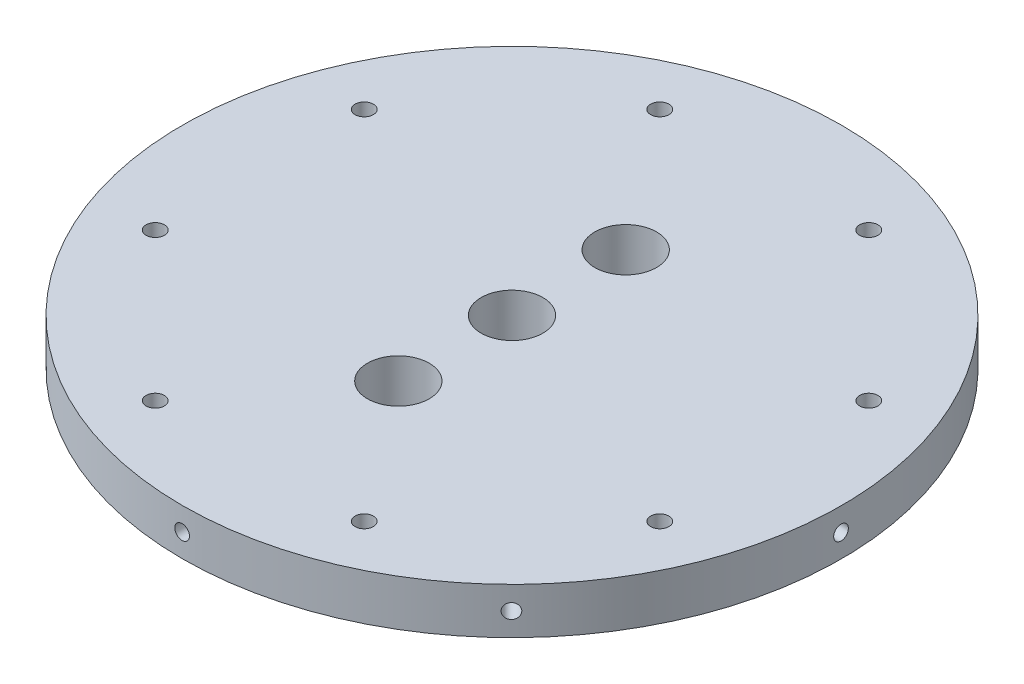
SolidWorks part; units mm, degrees
material "6061-T6 (SS)"
ref_plane "Front Plane" through (0, 0, 0) normal (0, 0, 1) x (1, 0, 0)
ref_plane "Top Plane" through (0, 0, 0) normal (0, 1, 0) x (1, 0, 0)
ref_plane "Right Plane" through (0, 0, 0) normal (1, 0, 0) x (0, 0, -1)
sketch "Sketch1" plane through (0, 0, 0) normal (0, 1, 0) x (1, 0, 0)
  circle A0 centre (0, 0) radius 50.8
  dimension "D1" = 101.6
extrude "Boss-Extrude1" add sketch "Sketch1" along normal blind 7.112 contours A0
sketch "Sketch2" plane through (0, 0, 0) normal (0, -1, 0) x (1, 0, 0)
  line L0 (0, 0) -> (-50.8, 0) construction
  line L1 (0, -17.526) -> (0, 17.526) construction
  circle A0 centre (0, 0) radius 50.8 construction
  circle A1 centre (0, 17.526) radius 4.7625
  circle A2 centre (0, 0) radius 4.7625
  circle A3 centre (0, -17.526) radius 4.7625
  point P9 (0, 0)
  dimension "D1" = 9.525
  dimension "D3" = 9.525
  dimension "D4" = 9.525
  dimension "D2" = 35.052
extrude "Cut-Extrude1" cut sketch "Sketch2" against normal through all contours A2 | A3 | A1
ref_plane "Plane1" through (0, 0, 50.8) normal (0, 0, 1) x (1, 0, 0)
hole_wizard "#4-40 Tapped Hole1" positions "3DSketch4" profile "Sketch8" tap size "#4-40" standard "ANSI Inch"
sketch3d "3DSketch4"
  point P0 (17.0245, 10.3666, 0)
  point P2 (17.0245, 10.3666, 0)
  point P4 (17.0245, 10.3666, 0)
  point P6 (17.0245, 10.3666, 0)
  point P8 (17.0245, 10.3666, 0)
  point P10 (17.0245, 10.3666, 0)
  point P12 (17.0245, 10.3666, 0)
  point P14 (17.0245, 10.3666, 0)
  point P16 (17.0245, 10.3666, 0)
  point P18 (-0.0622, 3.5544, 50.8)
sketch "Sketch8" plane through (-0.0622, 3.5544, 50.8) normal (0, 1, 0) x (1, 0, 0.0012)
  line L0 (0, 0) -> (0, 10.2042)
  line L1 (0, 10.2042) -> (1.1303, 9.525)
  line L2 (1.1303, 9.525) -> (1.1303, 0)
  line L3 (50.8, 50.8) -> (-50.8, 50.8) construction
  line L5 (1.1303, 0) -> (0, 0)
  line L10 (0, 10.2042) -> (-1.1303, 9.525) construction
  line L11 (0, 0) -> (0, 101.6) construction
  circle A0 centre (0, 50.8) radius 50.8 construction
  dimension "Tap Drill Dia." = 2.2606
  dimension "Tap Drill Depth" = 9.525
  dimension "Drill Angle" = 118
cosmetic thread "Hole Thread1" parameters "D1"=9.525, "D2"=2.8448
pattern_circular "CirPattern7" count 8 over 360 about axis through (0, 7.112, 0) along (0, 1, 0) of "#4-40 Tapped Hole1"
cosmetic thread "Hole Thread2" parameters "D1"=9.525, "D2"=2.8448
cosmetic thread "Hole Thread3" parameters "D1"=9.525, "D2"=2.8448
cosmetic thread "Hole Thread4" parameters "D1"=9.525, "D2"=2.8448
cosmetic thread "Hole Thread5" parameters "D1"=9.525, "D2"=2.8448
cosmetic thread "Hole Thread6" parameters "D1"=9.525, "D2"=2.8448
cosmetic thread "Hole Thread7" parameters "D1"=9.525, "D2"=2.8448
cosmetic thread "Hole Thread8" parameters "D1"=9.525, "D2"=2.8448
sketch "Sketch11" plane through (0, 7.112, 0) normal (0, 1, 0) x (1, 0, 0)
  line L0 (0, 0) -> (-50.8, 0) construction
  line L1 (0, 0) -> (-38.8924, 16.1098) construction
  circle A0 centre (0, 0) radius 42.0968 construction
  circle A1 centre (-38.8924, 16.1098) radius 1.4122
  circle A3 centre (0, 0) radius 50.8 construction
  dimension "D1" = 84.1936
  dimension "D2" = 2.8245
  dimension "D3" = 22.5
extrude "Cut-Extrude3" cut sketch "Sketch11" against normal through all contours A1
pattern_circular "CirPattern8" count 8 over 360 about axis through (0, 0, 0) along (0, 1, 0) of "Cut-Extrude3"
equation "\"0..28in\"=0.1"
